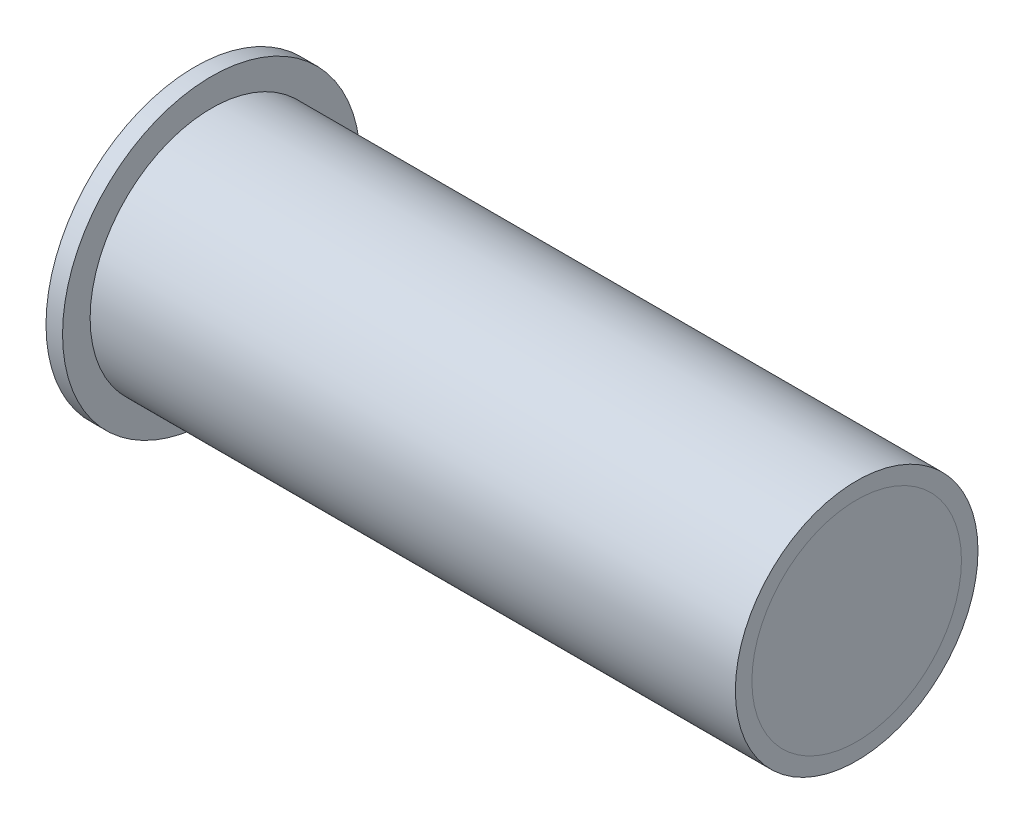
SolidWorks part; units mm, degrees
ref_plane "Front Plane" through (0, 0, 0) normal (0, 0, 1) x (1, 0, 0)
ref_plane "Top Plane" through (0, 0, 0) normal (0, 1, 0) x (1, 0, 0)
ref_plane "Right Plane" through (0, 0, 0) normal (1, 0, 0) x (0, 0, -1)
sketch "Sketch1" plane through (0, 0, 0) normal (0, 0, 1) x (1, 0, 0)
  line L0 (203.9697, 27) -> (203.9697, 19)
  line L1 (206.9697, 27) -> (129.9697, 27) construction
  line L2 (203.9697, 19) -> (323.9697, 19)
  line L3 (206.9697, 27) -> (206.9697, -27) construction
  line L4 (209.9697, 22) -> (206.9697, 22) construction
  line L6 (194, 0) -> (206.9697, 0) construction
  dimension "D1" = 3
  dimension "D2" = 3
  dimension "D3" = 120
revolve "Revolve-Thin1" add sketch "Sketch1" angle 360 about L6 wall 3
sketch "Sketch2" plane through (203.9697, 0, 0) normal (-1, 0, 0) x (0, 0, 1)
  circle A0 centre (0, 0) radius 19 construction
  circle A1 centre (0, 0) radius 19
extrude "Boss-Extrude1" add sketch "Sketch2" against normal blind 3 separate body
sketch "Sketch3" plane through (323.9697, 0, 0) normal (1, 0, 0) x (0, 0, -1)
  circle A0 centre (0, 0) radius 19 construction
  circle A1 centre (0, 0) radius 19
extrude "Boss-Extrude2" add sketch "Sketch3" against normal blind 3 separate body
